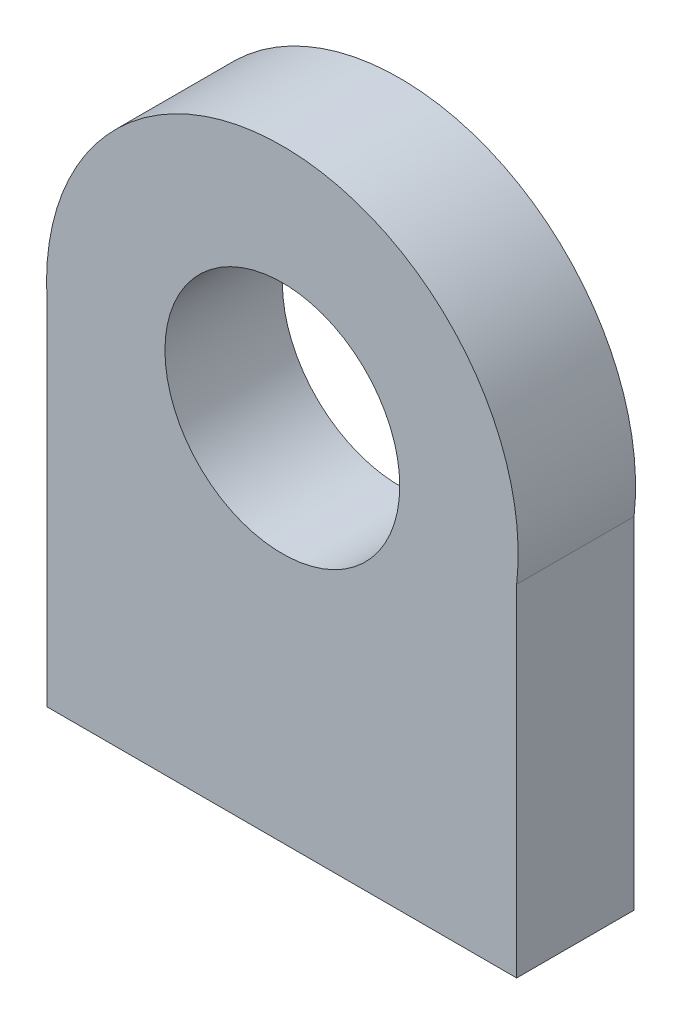
SolidWorks part; units mm, degrees
ref_plane "Alzado" through (0, 0, 0) normal (0, 0, 1) x (1, 0, 0)
ref_plane "Planta" through (0, 0, 0) normal (0, 1, 0) x (1, 0, 0)
ref_plane "Vista lateral" through (0, 0, 0) normal (1, 0, 0) x (0, 0, -1)
sketch "Croquis1" plane through (0, 0, 0) normal (0, 0, 1) x (1, 0, 0)
  line L7 (-21.862, -15.0002) -> (18.138, -15.0002)
  line L8 (18.138, -15.0002) -> (18.138, 14.9998)
  line L9 (-21.862, -15.0002) -> (-21.862, 14.9998)
  arc A0 (18.138, 14.9998) -> (17.3075, 22.1635) centre (-1.8186, 16.3161) ccw
  arc A1 (18.138, 14.9998) -> (17.3075, 22.1635) centre (-1.8186, 16.3161) ccw
  arc A2 (18.138, 14.0354) -> (-21.862, 14.9998) centre (-1.8186, 16.3161) ccw
  circle A3 centre (-1.8186, 16.3161) radius 10
  dimension "D4" = 40
  dimension "D5" = 20
  dimension "D1" = 40
  dimension "D2" = 30
  dimension "D3" = 30
extrude "Saliente-Extruir1" add sketch "Croquis1" along normal blind 10
